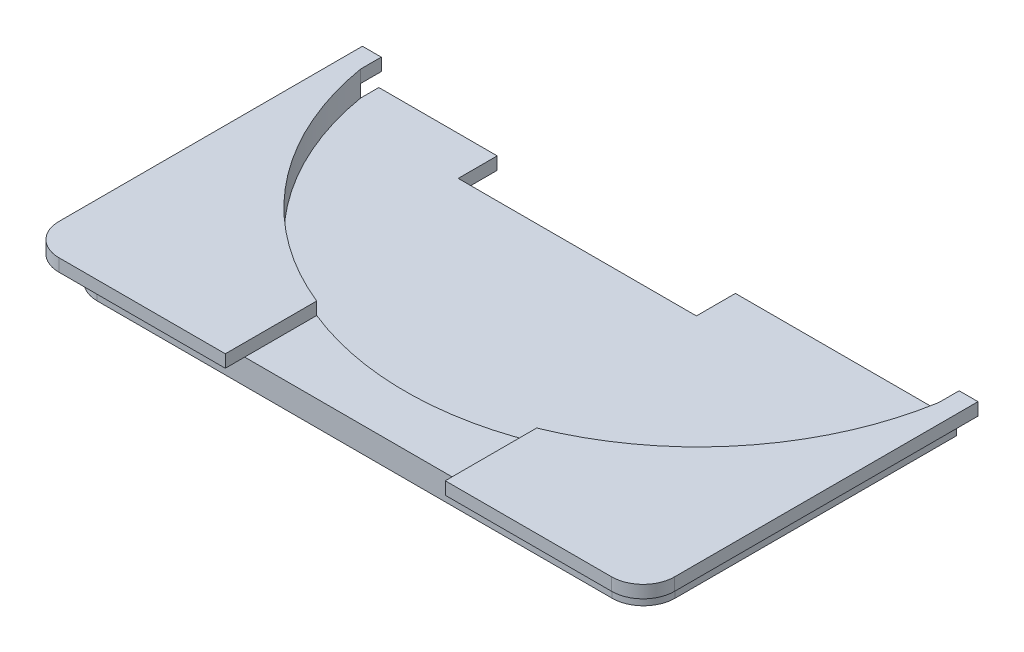
SolidWorks part; units mm, degrees
ref_plane "Front Plane" through (0, 0, 0) normal (0, 0, 1) x (1, 0, 0)
ref_plane "Top Plane" through (0, 0, 0) normal (0, 1, 0) x (1, 0, 0)
ref_plane "Right Plane" through (0, 0, 0) normal (1, 0, 0) x (0, 0, -1)
sketch "Sketch4" plane through (0, 0, 0) normal (0, 1, 0) x (1, 0, 0)
  line L1 (-107.0357, 49.142) -> (-15.0357, 49.142)
  line L2 (-107.0357, 49.142) -> (-107.0357, -45.858)
  line L3 (-102.0357, -50.858) -> (-20.0357, -50.858)
  line L4 (-15.0357, 49.142) -> (-15.0357, -45.858)
  arc A0 (-20.0357, -50.858) -> (-15.0357, -45.858) centre (-20.0357, -45.858) ccw
  arc A1 (-107.0357, -45.858) -> (-102.0357, -50.858) centre (-102.0357, -45.858) ccw
  point P6 (-15.0357, -50.858)
  point P9 (-107.0357, -50.858)
  dimension "D3" = 5
  dimension "D1" = 92
  dimension "D2" = 100
extrude "Boss-Extrude2" add sketch "Sketch4" along normal blind 4
sketch "Sketch5" plane through (0, 4, 0) normal (0, 1, 0) x (1, 0, 0)
  line L1 (-122.1841, 54.3122) -> (-0.8811, 54.3122)
  line L3 (-122.1841, 54.3122) -> (-116.2059, -1.7638)
  line L4 (-116.2059, -1.7638) -> (-107.0357, -1.7638)
  line L5 (-15.0357, -1.7638) -> (-0.8811, -1.7638)
  line L6 (-0.8811, -1.7638) -> (-0.8811, 54.3122)
  line L7 (-107.0357, 49.142) -> (-107.0357, -45.858) construction
  line L8 (-15.0357, -45.858) -> (-15.0357, 49.142) construction
  arc A0 (-15.0357, -1.7638) -> (-107.0357, -1.7638) centre (-61.0357, 1.9398) ccw
extrude "Cut-Extrude3" cut sketch "Sketch5" against normal blind 4
sketch "Sketch6" plane through (0, 4, 0) normal (0, 1, 0) x (1, 0, 0)
  circle A1 centre (-61.0392, 3.842) radius 46.6449
extrude "Cut-Extrude4" cut sketch "Sketch6" against normal blind 2
sketch "Sketch7" plane through (0, 2, 0) normal (0, 1, 0) x (1, 0, 0)
  line L1 (-50.2681, 14.744) -> (-88.1898, 14.744)
  line L2 (-50.2681, 14.744) -> (-50.2681, -7.222)
  line L3 (-50.2681, -7.222) -> (-88.1898, -7.222)
  line L4 (-88.1898, 14.744) -> (-88.1898, -7.222)
extrude "Cut-Extrude5" cut sketch "Sketch7" against normal blind 2
sketch "Sketch8" plane through (0, 2, 0) normal (0, 1, 0) x (1, 0, 0)
  line L2 (-107.0357, 51.8234) -> (-12.0357, 51.8234)
  line L3 (-12.0357, -0.1264) -> (-12.0357, 47.142) construction
  line L4 (-107.0357, -1.0114) -> (-15.0357, -1.0114)
  line L5 (-107.0357, 5.6435) -> (-107.0357, -3.9084) construction
  line L6 (-15.0357, -3.8667) -> (-15.0357, 5.6435) construction
  line L7 (-15.0357, -1.0114) -> (-12.0357, 51.8234)
  line L8 (-107.0357, 51.8234) -> (-107.0357, -1.0114)
extrude "Cut-Extrude7" cut sketch "Sketch8" against normal blind 10
sketch "Sketch10" plane through (0, 4, 0) normal (0, 1, 0) x (1, 0, 0)
  line L0 (-110.0357, -0.1264) -> (-110.0357, -48.858) construction
  line L1 (-110.0357, -0.6264) -> (-107.0357, -0.6264)
  line L2 (-110.0357, -0.6264) -> (-110.0357, -48.9393)
  line L3 (-105.0357, -53.9393) -> (-78.5477, -53.9393)
  line L4 (-12.0357, -0.6264) -> (-12.0357, -48.9393)
  line L5 (-12.0357, -42.627) -> (-12.0357, -48.7314) construction
  line L6 (-110.0357, -0.1264) -> (-106.6168, -0.1264) construction
  line L8 (-107.0357, -3.9084) -> (-107.0357, -0.6264)
  line L9 (-107.0357, -0.1264) -> (-107.0357, -45.858) construction
  line L10 (-15.0357, -3.8667) -> (-15.0357, -0.6264)
  line L11 (-15.0357, -0.6264) -> (-12.0357, -0.6264)
  line L14 (-78.5477, -53.9393) -> (-78.5477, -39.3923)
  line L16 (-43.5308, -53.9393) -> (-43.5308, -39.3923)
  line L20 (-43.5308, -53.9393) -> (-17.0357, -53.9393)
  arc A1 (-107.0357, -3.9084) -> (-78.5477, -39.3923) centre (-61.0392, 3.842) ccw
  arc A3 (-43.5308, -39.3923) -> (-15.0357, -3.8667) centre (-61.0392, 3.842) ccw
  arc A4 (-17.0357, -53.9393) -> (-12.0357, -48.9393) centre (-17.0357, -48.9393) ccw
  arc A5 (-110.0357, -48.9393) -> (-105.0357, -53.9393) centre (-105.0357, -48.9393) ccw
  point P13 (-61.0392, -47.565)
  point P28 (-12.0357, -53.9393)
  dimension "D2" = 5
  dimension "D1" = 0.5
extrude "Boss-Extrude3" add sketch "Sketch10" along normal blind 2
